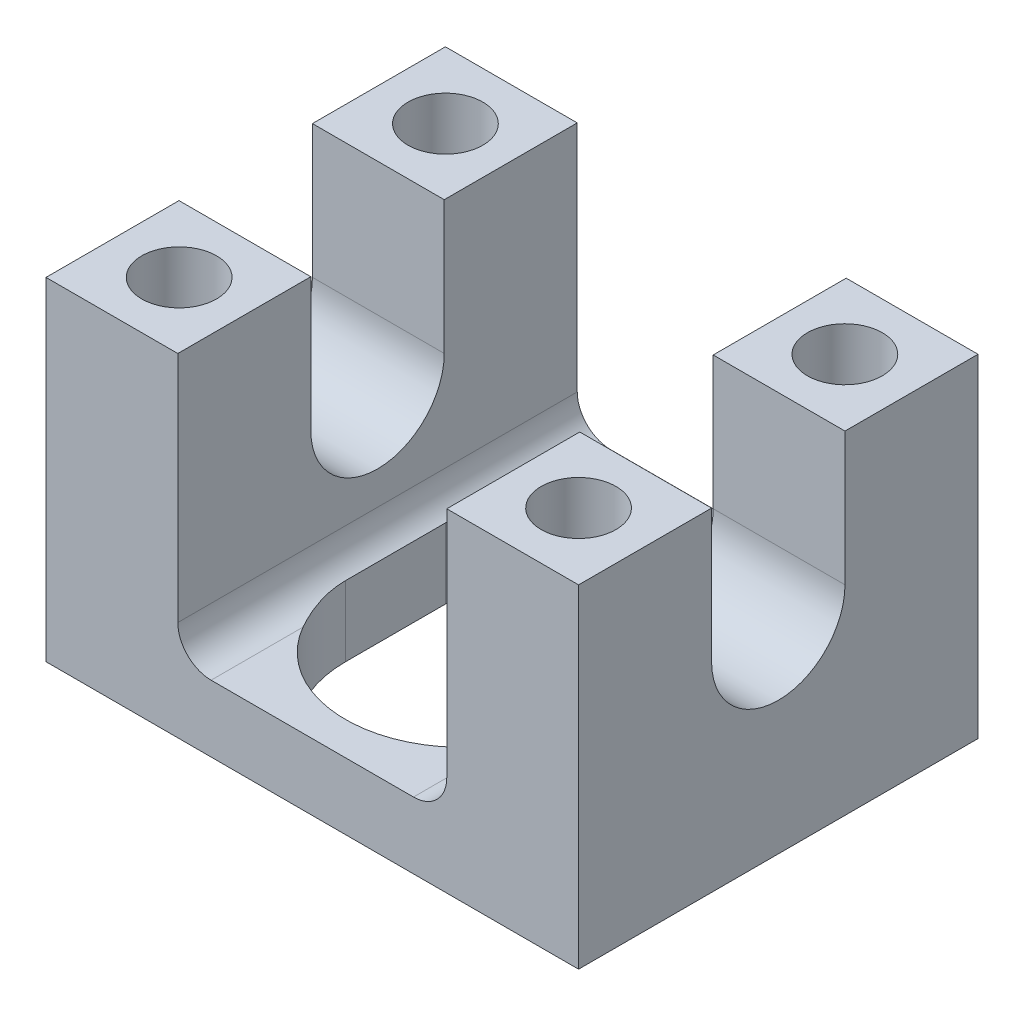
SolidWorks part; units mm, degrees
material "NITRONIC 60"
ref_plane "XY" through (0, 0, 0) normal (0, 0, 1) x (1, 0, 0)
ref_plane "XZ" through (0, 0, 0) normal (0, 1, 0) x (1, 0, 0)
ref_plane "YZ" through (0, 0, 0) normal (1, 0, 0) x (0, 0, -1)
sketch "Sketch1" plane through (0, 0, 0) normal (0, 0, 1) x (1, 0, 0)
  line L0 (25.4, 15.875) -> (-25.4, -15.875) construction
  line L1 (25.4, 15.875) -> (12.827, 15.875)
  line L2 (25.4, 15.875) -> (25.4, -15.875)
  line L3 (25.4, -15.875) -> (-25.4, -15.875)
  line L4 (-25.4, 15.875) -> (-25.4, -15.875)
  line L5 (12.827, 15.875) -> (12.827, -9.525)
  line L6 (12.827, -9.525) -> (-12.827, -9.525)
  line L7 (-12.827, -9.525) -> (-12.827, 15.875)
  line L8 (-12.827, 15.875) -> (-25.4, 15.875)
  line L9 (0, 0) -> (0, 6.9368) construction
  dimension "D1" = 50.8
  dimension "D2" = 31.75
  dimension "D3" = 25.654
  dimension "D4" = 6.35
extrude "Extrude1" add sketch "Sketch1" along normal mid plane 38.1
sketch "Sketch2" plane through (-25.4, 0, 0) normal (-1, 0, 0) x (0, 0, 1)
  line L0 (-6.3627, 15.875) -> (-6.3627, 3.175)
  line L1 (19.05, 15.875) -> (-19.05, 15.875) construction
  line L2 (6.3627, 15.875) -> (6.3627, 3.175)
  line L3 (0, 0) -> (0, 4.5699) construction
  line L4 (6.3627, 15.875) -> (-6.3627, 15.875)
  arc A0 (-6.3627, 3.175) -> (6.3627, 3.175) centre (0, 3.175) ccw
  circle A1 centre (0, 3.175) radius 6.3627 construction
  dimension "D1" = 12.7254
  dimension "D2" = 12.7
extrude "Cut-Extrude1" cut sketch "Sketch2" against normal through all
fillet "Fillet1" radius 3.175 2 edges at (12.827, -9.525, 0) (-12.827, -9.525, 0)
sketch "Sketch3" plane through (0, -9.525, 0) normal (0, 1, 0) x (-1, 0, 0)
  line L0 (-11.1125, 4.7752) -> (-11.1125, -4.7752)
  line L1 (-11.1125, -4.7752) -> (11.1125, -4.7752) construction
  line L2 (-11.1125, 4.7752) -> (11.1125, 4.7752) construction
  line L3 (11.1125, 4.7752) -> (11.1125, -4.7752)
  arc A1 (-11.1125, -4.7752) -> (11.1125, -4.7752) centre (0, -4.7752) ccw
  arc A2 (11.1125, 4.7752) -> (-11.1125, 4.7752) centre (0, 4.7752) ccw
extrude "Cut-Extrude2" cut sketch "Sketch3" against normal through all and the other way blind 2.54
sketch "Sketch4" plane through (0, 15.875, 0) normal (0, 1, 0) x (-1, 0, 0)
  line L0 (0, -2.8038) -> (0, 6.955) construction
  line L1 (-4.7702, 0) -> (5.2071, 0) construction
  circle A0 centre (-19.05, -12.7) radius 3.5687
  circle A1 centre (-19.05, 12.7) radius 3.5687
  circle A2 centre (19.05, 12.7) radius 3.5687
  circle A3 centre (19.05, -12.7) radius 3.5687
  dimension "D1" = 7.1374
  dimension "D2" = 25.4
  dimension "D3" = 38.1
extrude "Cut-Extrude3" cut sketch "Sketch4" against normal through all
